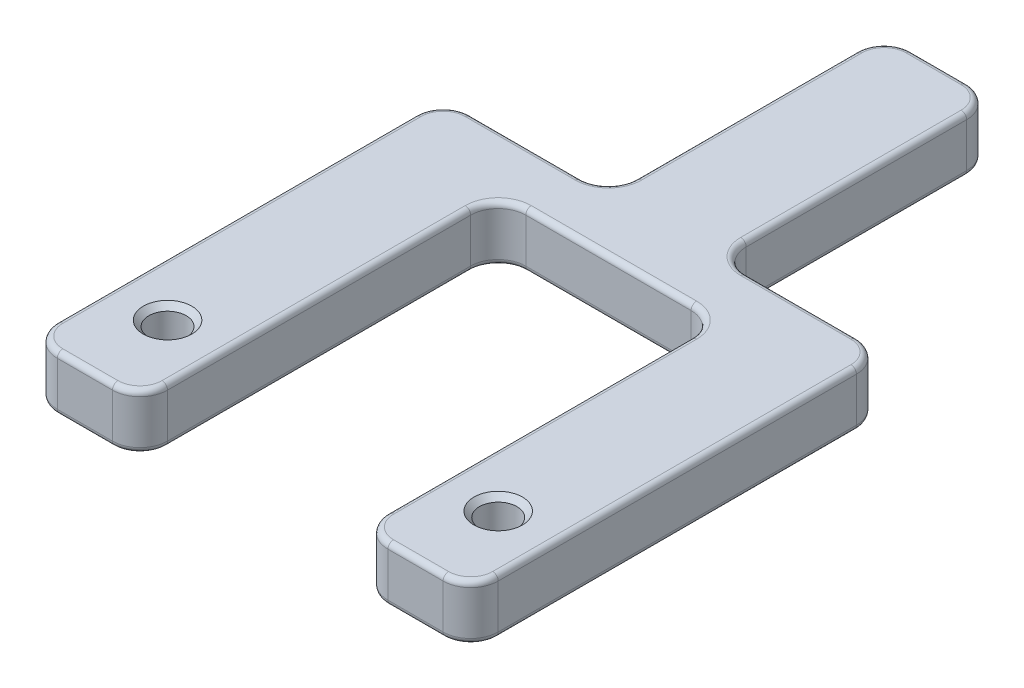
SolidWorks part; units mm, degrees
ref_plane "Front Plane" through (0, 0, 0) normal (0, 0, 1) x (1, 0, 0)
ref_plane "Top Plane" through (0, 0, 0) normal (0, 1, 0) x (1, 0, 0)
ref_plane "Right Plane" through (0, 0, 0) normal (1, 0, 0) x (0, 0, -1)
sketch "Sketch3" plane through (0, 0, 0) normal (0, 1, 0) x (1, 0, 0)
  line L0 (0, 55) -> (0, 25)
  line L1 (0, 25) -> (-10, 25)
  line L2 (-10, 25) -> (-10, -7.5)
  line L3 (-10, -7.5) -> (-20, -7.5)
  line L4 (-20, -7.5) -> (-20, 30)
  line L5 (-20, 30) -> (-5, 30)
  line L6 (-5, 30) -> (-5, 55)
  line L7 (-5, 55) -> (0, 55)
  point P9 (-15, -7.5)
  dimension "D1" = 15
  dimension "D2" = 25
  dimension "D3" = 5
  dimension "D4" = 5
  dimension "D5" = 25
  dimension "D6" = 10
  dimension "D7" = 7.5
extrude "Boss-Extrude1" add sketch "Sketch3" along normal blind 5
mirror "Mirror1" about plane through (0, 0, 0) normal (1, 0, 0) of "Boss-Extrude1"
hole_wizard "M3 Clearance Hole1" positions "Sketch4" profile "Sketch5" hole size "M3" standard "ANSI Metric"
sketch "Sketch4" plane through (0, 5, 0) normal (0, 1, 0) x (1, 0, 0)
  line L0 (-15, 0) -> (15, 0) construction
  point P0 (-15, 0)
  point P2 (15, 0)
  point P9 (0, 0)
  dimension "D1" = 30
sketch "Sketch5" plane through (-15, 5, 0) normal (1, 0, 0) x (0, 0, 1)
  line L0 (0, 0) -> (0, 6.0215)
  line L1 (0, 6.0215) -> (1.7, 5)
  line L2 (1.7, 5) -> (1.7, 0)
  line L5 (1.7, 0) -> (0, 0)
  line L10 (0, 6.0215) -> (-1.7, 5) construction
  line L11 (0, -6.35) -> (0, 107.95) construction
  dimension "Hole Dia." = 3.4
  dimension "Hole Depth" = 5
  dimension "Drill Angle" = 118
fillet "Fillet1" radius 2.5 12 edges at (-5, 2.5, -30) (-20, 2.5, -30) (-5, 2.5, -55) (5, 2.5, -55) (5, 2.5, -30) (20, 2.5, -30) (20, 2.5, 7.5) (10, 2.5, 7.5) (10, 2.5, -25) (-10, 2.5, -25) (-10, 2.5, 7.5) (-20, 2.5, 7.5)
chamfer "Chamfer1" distance 0.5 angle 45 4 edges at (15, 0, -1.7) (-15, 0, -1.7) (15, 5, 1.7) (-15, 5, 1.7)
fillet "Fillet2" radius 0.5 48 edges at (-19.2678, 5, -29.2678) (-12.5, 5, -30) (-5.7322, 5, -30.7322) (-5, 5, -42.5) (-4.2678, 5, -54.2678) (0, 5, -55) (4.2678, 5, -54.2678) (5, 0, -42.5) (5, 5, -42.5) (5.7322, 5, -30.7322) (12.5, 0, -30) (12.5, 5, -30) (19.2678, 5, -29.2678) (20, 0, -11.25) (20, 5, -11.25) (19.2678, 5, 6.7678) (15, 0, 7.5) (15, 5, 7.5) (10.7322, 5, 6.7678) (10, 0, -8.75) (10, 5, -8.75) (9.2678, 5, -24.2678) (0, 5, -25) (-9.2678, 5, -24.2678) (-10, 5, -8.75) (-10.7322, 5, 6.7678) (-15, 5, 7.5) (-19.2678, 5, 6.7678) (-4.2678, 0, -54.2678) (0, 0, -55) (4.2678, 0, -54.2678) (5.7322, 0, -30.7322) (19.2678, 0, -29.2678) (19.2678, 0, 6.7678) (10.7322, 0, 6.7678) (9.2678, 0, -24.2678) (0, 0, -25) (-9.2678, 0, -24.2678) (-10, 0, -8.75) (-10.7322, 0, 6.7678) (-15, 0, 7.5) (-19.2678, 0, 6.7678) (-20, 0, -11.25) (-19.2678, 0, -29.2678) (-12.5, 0, -30) (-5.7322, 0, -30.7322) (-20, 5, -11.25) (-5, 0, -42.5)
